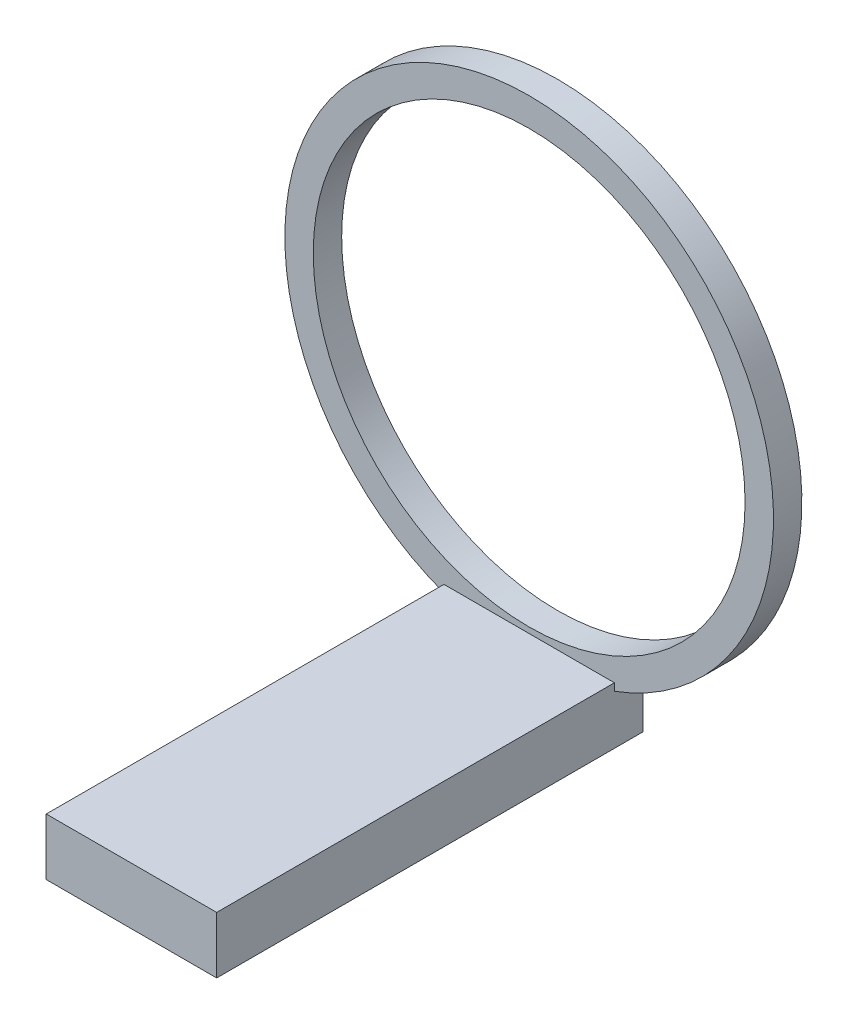
SolidWorks part; units mm, degrees
ref_plane "Front Plane" through (0, 0, 0) normal (0, 0, 1) x (1, 0, 0)
ref_plane "Top Plane" through (0, 0, 0) normal (0, 1, 0) x (1, 0, 0)
ref_plane "Right Plane" through (0, 0, 0) normal (1, 0, 0) x (0, 0, -1)
sketch "Sketch1" plane through (0, 0, 0) normal (0, 0, 1) x (1, 0, 0)
  line L0 (-19.05, -12.7) -> (-19.05, 0)
  line L1 (-19.05, -12.7) -> (19.05, -12.7)
  line L2 (-19.05, 0) -> (19.05, 0)
  line L3 (19.05, -12.7) -> (19.05, 0)
  line L4 (-19.05, -12.7) -> (19.05, 0) construction
  line L5 (-19.05, 0) -> (19.05, -12.7) construction
  point P0 (0, -16.0867)
  point P1 (0, -6.35)
  dimension "D1" = 12.7
  dimension "D2" = 38.1
extrude "Boss-Extrude1" add sketch "Sketch1" along normal blind 95.25
sketch "Sketch2" plane through (0, 0, 0) normal (0, 0, -1) x (-1, 0, 0)
  line L0 (0, 0) -> (0, 49.53) construction
  circle A0 centre (0, 49.53) radius 54.61
  circle A1 centre (0, 49.53) radius 48.26
  dimension "D2" = 109.22
  dimension "D3" = 96.52
  dimension "D1" = 49.53
extrude "Boss-Extrude2" add sketch "Sketch2" against normal blind 6.35
